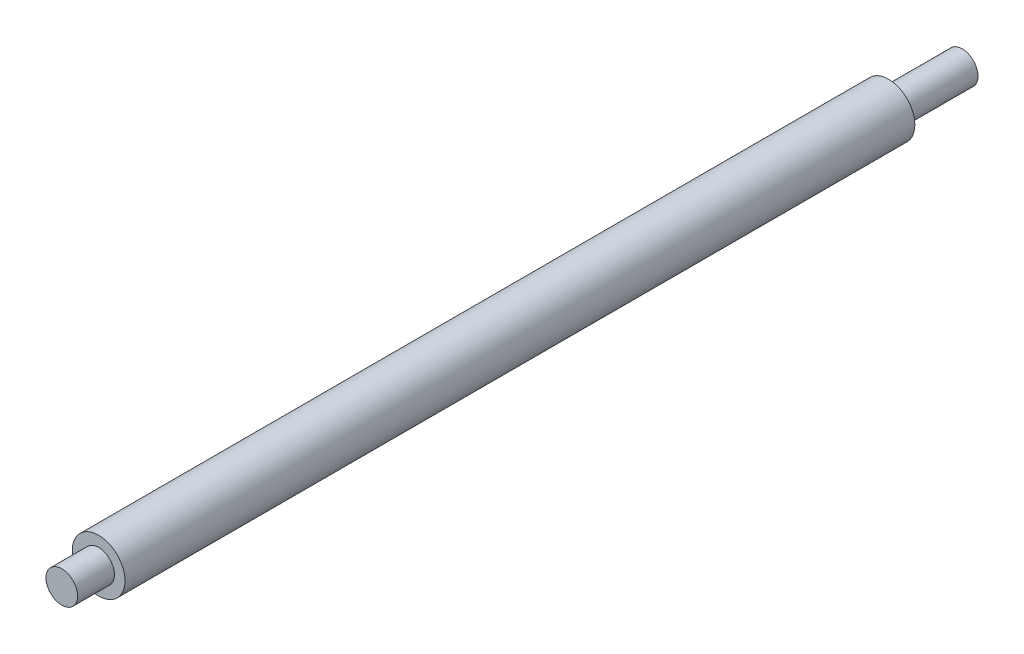
SolidWorks part; units mm, degrees
ref_plane "Front Plane" through (0, 0, 0) normal (0, 0, 1) x (1, 0, 0)
ref_plane "Top Plane" through (0, 0, 0) normal (0, 1, 0) x (1, 0, 0)
ref_plane "Right Plane" through (0, 0, 0) normal (1, 0, 0) x (0, 0, -1)
sketch "Sketch1" plane through (0, 0, 0) normal (0, 0, 1) x (1, 0, 0)
  circle A0 centre (0, 0) radius 25
  point P3 (0, 0)
  point P4 (0, 0)
  dimension "D1" = 50
extrude "Boss-Extrude2" add sketch "Sketch1" along normal blind 750
sketch "Sketch2" plane through (0, 0, 0) normal (0, 0, -1) x (-1, 0, 0)
  circle A0 centre (0, 0) radius 15
extrude "Boss-Extrude3" add sketch "Sketch2" along normal blind 70
sketch "Sketch3" plane through (0, 0, 750) normal (0, 0, 1) x (1, 0, 0)
  circle A0 centre (0, 0) radius 15
extrude "Boss-Extrude4" add sketch "Sketch3" along normal blind 35
